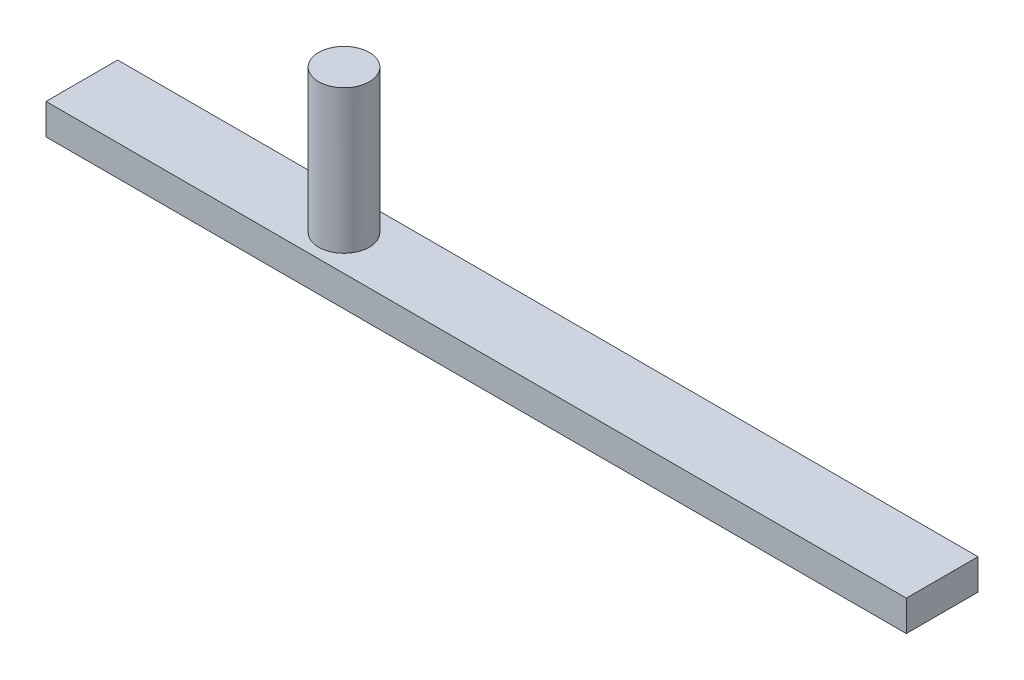
SolidWorks part; units mm, degrees
material "Pine"
ref_plane "Front Plane" through (0, 0, 0) normal (0, 0, 1) x (1, 0, 0)
ref_plane "Top Plane" through (0, 0, 0) normal (0, 1, 0) x (1, 0, 0)
ref_plane "Right Plane" through (0, 0, 0) normal (1, 0, 0) x (0, 0, -1)
sketch "Sketch1" plane through (0, 0, 0) normal (0, 1, 0) x (1, 0, 0)
  line L1 (0, 0) -> (1066.8, 0)
  line L2 (0, 0) -> (0, 88.9)
  line L3 (0, 88.9) -> (1066.8, 88.9)
  line L4 (1066.8, 0) -> (1066.8, 88.9)
  dimension "D1" = 88.9
  dimension "D2" = 1066.8
extrude "Boss-Extrude1" add sketch "Sketch1" along normal blind 38.1
sketch "Sketch2" plane through (0, 38.1, 0) normal (0, 1, 0) x (1, 0, 0)
  circle A0 centre (325.6715, 43.8548) radius 31.428
extrude "Boss-Extrude2" add sketch "Sketch2" along normal blind 177.8
